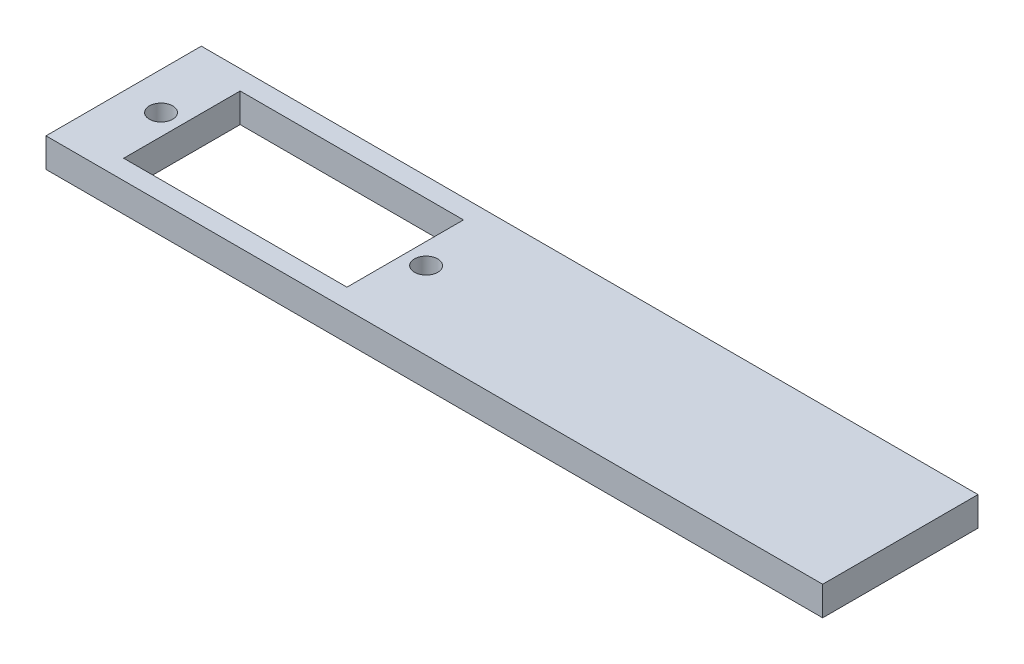
SolidWorks part; units mm, degrees
ref_plane "Front Plane" through (0, 0, 0) normal (0, 0, 1) x (1, 0, 0)
ref_plane "Top Plane" through (0, 0, 0) normal (0, 1, 0) x (1, 0, 0)
ref_plane "Right Plane" through (0, 0, 0) normal (1, 0, 0) x (0, 0, -1)
sketch "Sketch1" plane through (0, 0, 0) normal (0, 1, 0) x (1, 0, 0)
  line L1 (-40, -8) -> (40, -8)
  line L2 (-40, -8) -> (-40, 8)
  line L3 (-40, 8) -> (40, 8)
  line L4 (40, -8) -> (40, 8)
  line L5 (0, 8) -> (0, -8) construction
  line L6 (-40, 0) -> (40, 0) construction
  point P0 (0, 0)
  dimension "D1" = 16
  dimension "D2" = 80
extrude "Boss-Extrude1" add sketch "Sketch1" along normal blind 3
sketch "Sketch2" plane through (0, 3, 0) normal (0, 1, 0) x (1, 0, 0)
  line L4 (-40, 8) -> (-40, -8) construction
  line L5 (-34, -6) -> (-11, -6)
  line L6 (-34, -6) -> (-34, 6)
  line L7 (-34, 6) -> (-11, 6)
  line L8 (-11, -6) -> (-11, 6)
  line L9 (-22.5, 6) -> (-22.5, -6) construction
  line L10 (-34, 0) -> (-11, 0) construction
  circle A0 centre (-36.15, 0) radius 1.2
  circle A2 centre (-8.85, 0) radius 1.2
  point P0 (-22.5, 0)
  dimension "D4" = 2.4
  dimension "D5" = 2.15
  dimension "D6" = 27.3
  dimension "D1" = 12
  dimension "D2" = 23
  dimension "D3" = 6
extrude "Cut-Extrude1" cut sketch "Sketch2" against normal through all
